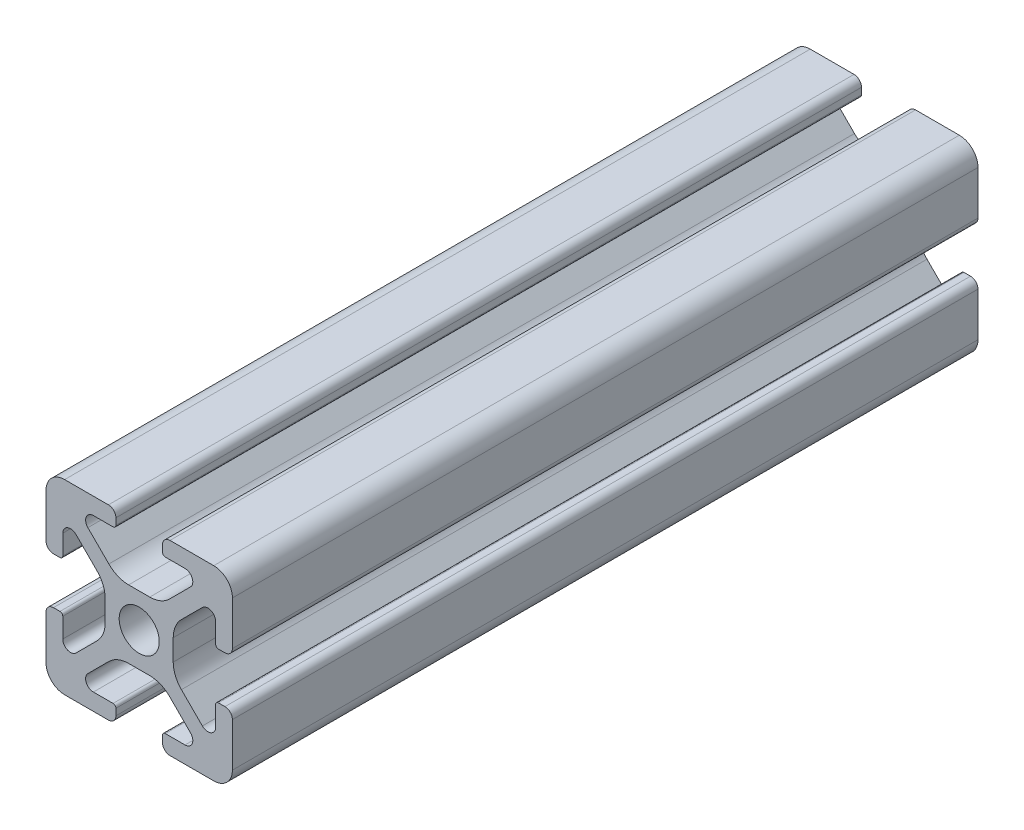
SolidWorks part; units mm, degrees
ref_plane "Front Plane" through (0, 0, 0) normal (0, 0, 1) x (1, 0, 0)
ref_plane "Top Plane" through (0, 0, 0) normal (0, 1, 0) x (1, 0, 0)
ref_plane "Right Plane" through (0, 0, 0) normal (1, 0, 0) x (0, 0, -1)
ref_plane "Plane1" through (0, 0, 0) normal (0, 0, -1) x (-1, 0, 0)
sketch "Sketch1" plane through (0, 0, 0) normal (0, 0, -1) x (-1, 0, 0)
  line L0 (-12.5, 0.8) -> (-12.5, 1.5)
  line L1 (-12.8, 1.8) -> (-14.9176, 1.8)
  line L2 (-15.5062, 3.221) -> (-13.2559, 5.4713)
  line L3 (-11.1346, 6.35) -> (-8.8654, 6.35)
  line L4 (-6.7441, 5.4713) -> (-4.4938, 3.221)
  line L5 (-5.0824, 1.8) -> (-7.2, 1.8)
  line L6 (-7.5, 1.5) -> (-7.5, 0.8)
  line L7 (-6.7, 0) -> (-2, 0)
  line L8 (0, 2) -> (0, 6.7)
  line L9 (-0.8, 7.5) -> (-1.5, 7.5)
  line L10 (-1.8, 7.2) -> (-1.8, 5.0824)
  line L11 (-3.221, 4.4938) -> (-5.4713, 6.7441)
  line L12 (-6.35, 8.8654) -> (-6.35, 11.1346)
  line L13 (-5.4713, 13.2559) -> (-3.221, 15.5062)
  line L14 (-1.8, 14.9176) -> (-1.8, 12.8)
  line L15 (-1.5, 12.5) -> (-0.8, 12.5)
  line L16 (0, 13.3) -> (0, 18)
  line L17 (-2, 20) -> (-6.7, 20)
  line L18 (-7.5, 19.2) -> (-7.5, 18.5)
  line L19 (-7.2, 18.2) -> (-5.0824, 18.2)
  line L20 (-4.4938, 16.779) -> (-6.7441, 14.5287)
  line L21 (-8.8654, 13.65) -> (-11.1346, 13.65)
  line L22 (-13.2559, 14.5287) -> (-15.5062, 16.779)
  line L23 (-14.9176, 18.2) -> (-12.8, 18.2)
  line L24 (-12.5, 18.5) -> (-12.5, 19.2)
  line L25 (-13.3, 20) -> (-18, 20)
  line L26 (-20, 18) -> (-20, 13.3)
  line L27 (-19.2, 12.5) -> (-18.5, 12.5)
  line L28 (-18.2, 12.8) -> (-18.2, 14.9176)
  line L29 (-16.779, 15.5062) -> (-14.5287, 13.2559)
  line L30 (-13.65, 11.1346) -> (-13.65, 8.8654)
  line L31 (-14.5287, 6.7441) -> (-16.779, 4.4938)
  line L32 (-18.2, 5.0824) -> (-18.2, 7.2)
  line L33 (-18.5, 7.5) -> (-19.2, 7.5)
  line L34 (-20, 6.7) -> (-20, 2)
  line L35 (-18, 0) -> (-13.3, 0)
  arc A0 (-12.5, 1.5) -> (-12.8, 1.8) centre (-12.8, 1.5) ccw
  arc A1 (-14.9176, 1.8) -> (-15.5062, 3.221) centre (-14.9176, 2.6324) cw
  arc A2 (-13.2559, 5.4713) -> (-11.1346, 6.35) centre (-11.1346, 3.35) cw
  arc A3 (-8.8654, 6.35) -> (-6.7441, 5.4713) centre (-8.8654, 3.35) cw
  arc A4 (-4.4938, 3.221) -> (-5.0824, 1.8) centre (-5.0824, 2.6324) cw
  arc A5 (-7.2, 1.8) -> (-7.5, 1.5) centre (-7.2, 1.5) ccw
  arc A6 (-7.5, 0.8) -> (-6.7, 0) centre (-6.7, 0.8) ccw
  arc A7 (-2, 0) -> (0, 2) centre (-2, 2) ccw
  arc A8 (0, 6.7) -> (-0.8, 7.5) centre (-0.8, 6.7) ccw
  arc A9 (-1.5, 7.5) -> (-1.8, 7.2) centre (-1.5, 7.2) ccw
  arc A10 (-1.8, 5.0824) -> (-3.221, 4.4938) centre (-2.6324, 5.0824) cw
  arc A11 (-5.4713, 6.7441) -> (-6.35, 8.8654) centre (-3.35, 8.8654) cw
  arc A12 (-6.35, 11.1346) -> (-5.4713, 13.2559) centre (-3.35, 11.1346) cw
  arc A13 (-3.221, 15.5062) -> (-1.8, 14.9176) centre (-2.6324, 14.9176) cw
  arc A14 (-1.8, 12.8) -> (-1.5, 12.5) centre (-1.5, 12.8) ccw
  arc A15 (-0.8, 12.5) -> (0, 13.3) centre (-0.8, 13.3) ccw
  arc A16 (0, 18) -> (-2, 20) centre (-2, 18) ccw
  arc A17 (-6.7, 20) -> (-7.5, 19.2) centre (-6.7, 19.2) ccw
  arc A18 (-7.5, 18.5) -> (-7.2, 18.2) centre (-7.2, 18.5) ccw
  arc A19 (-5.0824, 18.2) -> (-4.4938, 16.779) centre (-5.0824, 17.3676) cw
  arc A20 (-6.7441, 14.5287) -> (-8.8654, 13.65) centre (-8.8654, 16.65) cw
  arc A21 (-11.1346, 13.65) -> (-13.2559, 14.5287) centre (-11.1346, 16.65) cw
  arc A22 (-15.5062, 16.779) -> (-14.9176, 18.2) centre (-14.9176, 17.3676) cw
  arc A23 (-12.8, 18.2) -> (-12.5, 18.5) centre (-12.8, 18.5) ccw
  arc A24 (-12.5, 19.2) -> (-13.3, 20) centre (-13.3, 19.2) ccw
  arc A25 (-18, 20) -> (-20, 18) centre (-18, 18) ccw
  arc A26 (-20, 13.3) -> (-19.2, 12.5) centre (-19.2, 13.3) ccw
  arc A27 (-18.5, 12.5) -> (-18.2, 12.8) centre (-18.5, 12.8) ccw
  arc A28 (-18.2, 14.9176) -> (-16.779, 15.5062) centre (-17.3676, 14.9176) cw
  arc A29 (-14.5287, 13.2559) -> (-13.65, 11.1346) centre (-16.65, 11.1346) cw
  arc A30 (-13.65, 8.8654) -> (-14.5287, 6.7441) centre (-16.65, 8.8654) cw
  arc A31 (-16.779, 4.4938) -> (-18.2, 5.0824) centre (-17.3676, 5.0824) cw
  arc A32 (-18.2, 7.2) -> (-18.5, 7.5) centre (-18.5, 7.2) ccw
  arc A33 (-19.2, 7.5) -> (-20, 6.7) centre (-19.2, 6.7) ccw
  arc A34 (-20, 2) -> (-18, 0) centre (-18, 2) ccw
  arc A35 (-13.3, 0) -> (-12.5, 0.8) centre (-13.3, 0.8) ccw
  circle A36 centre (-10, 10) radius 2.15
extrude "Boss-Extrude1" add sketch "Sketch1" against normal blind 80
equation "\"motor_module_height\" = 80"
equation "\"motor_module_width\" = 80"
equation "\"motor_module_length\" = 170"
equation "\"D1@Boss-Extrude1\"=\"motor_module_height\""
